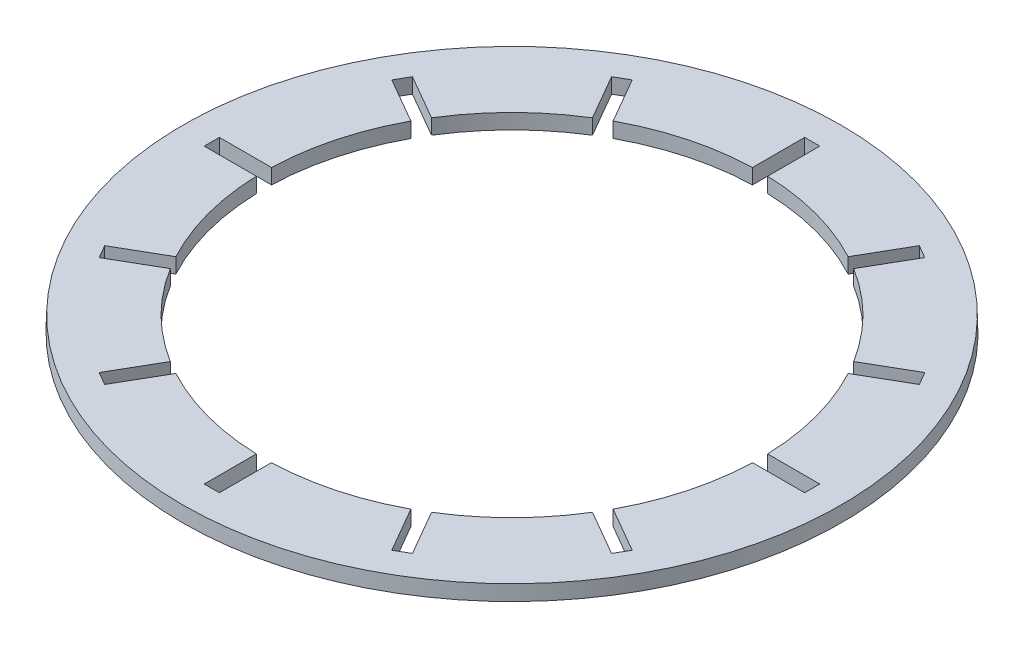
SolidWorks part; units mm, degrees
ref_plane "Front" through (0, 0, 0) normal (0, 0, 1) x (1, 0, 0)
ref_plane "Top" through (0, 0, 0) normal (0, 1, 0) x (1, 0, 0)
ref_plane "Right" through (0, 0, 0) normal (1, 0, 0) x (0, 0, -1)
sketch "Sketch1" plane through (0, 0, 0) normal (0, 1, 0) x (1, 0, 0)
  circle A0 centre (0, 0) radius 82.0755
  circle A1 centre (0, 0) radius 108.9786
  circle A2 centre (0, 0) radius 108.9786 construction
extrude "Boss-Extrude1" add sketch "Sketch1" along normal blind 5
sketch "Sketch2" plane through (0, 0, 0) normal (0, 0, 1) x (1, 0, 0)
  line L0 (108.9786, 0) -> (108.4682, 15.2115)
  line L1 (108.4682, 15.2115) -> (125.5641, 15.2115)
  line L2 (125.5641, 15.2115) -> (125.5641, 0)
  line L3 (125.5641, 0) -> (108.9786, 0)
  line L6 (0, 0) -> (0, 10.3268) construction
revolve "Cut-Revolve1" cut sketch "Sketch2" angle 360 about L6
sketch "Sketch3" plane through (0, 5, 0) normal (0, 1, 0) x (1, 0, 0)
  line L0 (0, 0) -> (177.1268, 0) construction
  line L2 (71.6668, -2.5) -> (99.2684, -2.5)
  line L3 (71.6668, -2.5) -> (71.6668, 2.5)
  line L4 (71.6668, 2.5) -> (99.2684, 2.5)
  line L5 (99.2684, -2.5) -> (99.2684, 2.5)
  line L6 (71.6668, -2.5) -> (99.2684, 2.5) construction
  line L7 (71.6668, 2.5) -> (99.2684, -2.5) construction
  point P4 (85.4676, 0)
  dimension "D1" = 5
extrude "Cut-Extrude1" cut sketch "Sketch3" against normal up to next (5 mm away)
pattern_circular "CirPattern1" count 12 every 30 about axis through (0, 0, 0) along (0, 1, 0) of "Cut-Extrude1"
